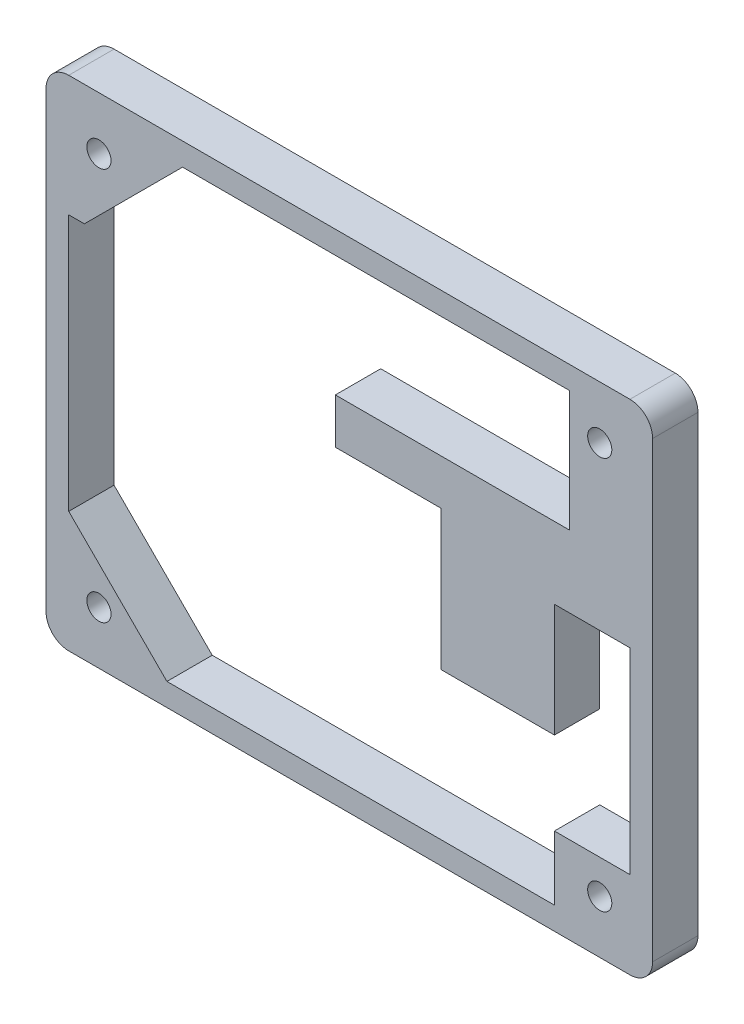
SolidWorks part; units mm, degrees
material "Acrylic (Medium-high impact)"
ref_plane "Front Plane" through (0, 0, 0) normal (0, 0, 1) x (1, 0, 0)
ref_plane "Top Plane" through (0, 0, 0) normal (0, 1, 0) x (1, 0, 0)
ref_plane "Right Plane" through (0, 0, 0) normal (1, 0, 0) x (0, 0, -1)
sketch "Sketch1" plane through (0, 0, 0) normal (0, 0, 1) x (1, 0, 0)
  line L1 (0, 0) -> (80.3, 0)
  line L2 (0, 0) -> (0, 66)
  line L3 (0, 66) -> (80.3, 66)
  line L4 (80.3, 0) -> (80.3, 66)
  dimension "D1" = 80.3
  dimension "D2" = 66
extrude "Boss-Extrude1" add sketch "Sketch1" along normal blind 6
hole_wizard "Ø3.2 (3.2) Diameter Hole1" positions "Sketch3" profile "Sketch2" hole size "Ø3.2" standard "ANSI Metric" end condition through all
sketch "Sketch3" plane through (0, 0, 6) normal (0, 0, 1) x (1, 0, 0)
  line L0 (0, 33) -> (80.3, 33) construction
  line L1 (0, 66) -> (0, 0) construction
  line L2 (80.3, 0) -> (80.3, 66) construction
  line L4 (7, 7) -> (7, 59) construction
  line L6 (7, 59) -> (73.3, 59) construction
  line L7 (73.3, 59) -> (73.3, 7) construction
  line L8 (73.3, 7) -> (7, 7) construction
  line L10 (40.15, 66) -> (40.15, 0) construction
  line L11 (80.3, 66) -> (0, 66) construction
  line L12 (0, 0) -> (80.3, 0) construction
  point P0 (7, 59)
  point P2 (73.3, 59)
  point P4 (73.3, 7)
  point P6 (7, 7)
  dimension "D1" = 66.3
  dimension "D2" = 52
  dimension "D3" = 26
  dimension "D4" = 33.15
sketch "Sketch2" plane through (7, 59, 6) normal (1, 0, 0) x (0, -1, 0)
  line L0 (0, 0) -> (0, 6)
  line L1 (0, 6) -> (1.6, 6)
  line L2 (1.6, 6) -> (1.6, 0)
  line L5 (1.6, 0) -> (0, 0)
  line L11 (0, -6.35) -> (0, 107.95) construction
  dimension "Thru Hole Dia." = 3.2
  dimension "Thru Hole Depth" = 6
fillet "Fillet1" radius 3 4 edges at (80.3, 66, 3) (80.3, 0, 3) (0, 0, 3) (0, 66, 3)
sketch "Sketch4" plane through (0, 0, 6) normal (0, 0, 1) x (1, 0, 0)
  line L0 (7, 59) -> (7, 7) construction
  line L1 (3, 16) -> (22, 16)
  line L2 (3, 16) -> (3, 50)
  line L3 (3, 50) -> (22, 50)
  line L4 (22, 16) -> (22, 50)
  line L5 (3, 33) -> (22, 33) construction
  line L6 (7, 59) -> (73.3, 59) construction
  line L7 (73.3, 59) -> (73.3, 7) construction
  line L8 (73.3, 7) -> (7, 7) construction
  line L9 (7, 33) -> (73.3, 33) construction
  line L10 (40.15, 59) -> (40.15, 7) construction
  line L11 (12.5, 50) -> (12.5, 16) construction
  line L13 (69.3, 63) -> (38.3, 63)
  line L14 (69.3, 63) -> (69.3, 47)
  line L15 (69.3, 47) -> (38.3, 47)
  line L16 (38.3, 63) -> (38.3, 47)
  line L17 (35, 56.5) -> (28, 56.5)
  line L18 (35, 56.5) -> (35, 49.5)
  line L19 (35, 49.5) -> (28, 49.5)
  line L20 (28, 56.5) -> (28, 49.5)
  line L21 (52.3, 41) -> (39.3, 41)
  line L22 (52.3, 41) -> (52.3, 24)
  line L23 (52.3, 24) -> (39.3, 24)
  line L24 (39.3, 41) -> (39.3, 24)
  line L25 (25.8294, 3) -> (65.8294, 3)
  line L26 (77.3, 37.5) -> (67.3, 37.5)
  line L27 (77.3, 37.5) -> (77.3, 11.5)
  line L28 (77.3, 11.5) -> (67.3, 11.5)
  line L29 (67.3, 37.5) -> (67.3, 11.5)
  line L30 (25.8294, 3) -> (25.8294, 22.5)
  line L31 (25.8294, 22.5) -> (65.8294, 22.5)
  line L32 (65.8294, 3) -> (65.8294, 22.5)
  dimension "D1" = 19
  dimension "D2" = 34
  dimension "D3" = 4
  dimension "D4" = 31
  dimension "D5" = 16
  dimension "D6" = 4
  dimension "D7" = 7
  dimension "D8" = 7
  dimension "D9" = 28
  dimension "D10" = 9.5
  dimension "D11" = 4
  dimension "D12" = 34
  dimension "D13" = 35
  dimension "D14" = 13
  dimension "D15" = 21
  dimension "D16" = 10
  dimension "D17" = 26
  dimension "D18" = 4
  dimension "D19" = 4.5
  dimension "D20" = 40
  dimension "D21" = 19.5
  dimension "D22" = 4
extrude "Cut-Extrude1" cut sketch "Sketch4" against normal through all
sketch "Sketch5" plane through (0, 0, 6) normal (0, 0, 1) x (1, 0, 0)
  line L0 (67.3, 11.5) -> (67.3, 3)
  line L1 (67.3, 3) -> (16, 3)
  line L2 (16, 3) -> (3, 16)
  line L3 (3, 16) -> (3, 50)
  line L4 (3, 50) -> (5.0711, 50)
  line L5 (18.0711, 63) -> (38.3, 63)
  line L6 (38.3, 63) -> (69.3, 63)
  line L7 (69.3, 63) -> (69.3, 47)
  line L8 (69.3, 47) -> (38.3, 47)
  line L9 (38.3, 47) -> (38.3, 41)
  line L10 (38.3, 41) -> (52.3, 41)
  line L12 (52.3, 41) -> (52.3, 22.5)
  line L13 (52.3, 22.5) -> (67.3, 22.5)
  line L15 (67.3, 37.5) -> (67.3, 11.5) construction
  line L16 (67.3, 22.5) -> (67.3, 11.5)
  line L17 (22, 50) -> (3, 50) construction
  line L18 (5.0711, 50) -> (18.0711, 63)
  line L19 (3, 16) -> (22, 16) construction
  line L20 (25.8294, 3) -> (65.8294, 3) construction
  line L21 (38.3, 63) -> (38.3, 47) construction
  line L22 (65.8294, 22.5) -> (25.8294, 22.5) construction
  circle A0 centre (7, 59) radius 1.6 construction
  dimension "D1" = 45
  dimension "D2" = 5
  dimension "D3" = 45
extrude "Cut-Extrude3" cut sketch "Sketch5" against normal through all
